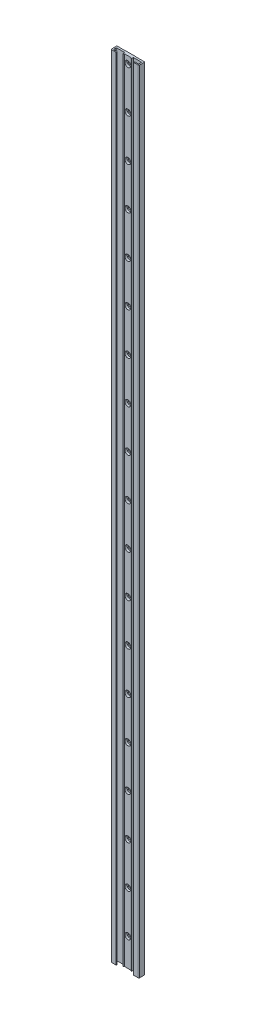
SolidWorks part; units mm, degrees
ref_plane "Front Plane" through (0, 0, 0) normal (0, 0, 1) x (1, 0, 0)
ref_plane "Top Plane" through (0, 0, 0) normal (0, 1, 0) x (1, 0, 0)
ref_plane "Right Plane" through (0, 0, 0) normal (1, 0, 0) x (0, 0, -1)
ref_plane "Plane4" through (0, 0, 8.7) normal (0, 0, 1) x (1, 0, 0)
sketch "Sketch1" plane through (0, 0, 8.7) normal (0, 0, 1) x (1, 0, 0)
  line L0 (-20, 0) -> (20, 0)
  line L1 (20, 0) -> (20, 1130.3)
  line L2 (20, 1130.3) -> (-20, 1130.3)
  line L3 (-20, 1130.3) -> (-20, 0)
  dimension "D1" = 1130.3
extrude "Boss-Extrude1" add sketch "Sketch1" against normal blind 8.7
sketch "Sketch2" plane through (0, 0, 0) normal (0, -1, 0) x (1, 0, 0)
  line L0 (12.5, 8.7) -> (-12.5, 8.7)
  line L1 (-12.5, 8.7) -> (-12.5, 7.2)
  line L2 (-12.5, 7.2) -> (-18, 7.2)
  line L3 (-18, 7.2) -> (-18, 2.8)
  line L4 (-18, 2.8) -> (-6.3, 2.8)
  line L5 (-6.3, 2.8) -> (-6.3, 5.5)
  line L6 (-6.3, 5.5) -> (-4.75, 5.5)
  line L7 (-4.75, 5.5) -> (-4.75, 4.5)
  line L8 (-4.75, 4.5) -> (4.75, 4.5)
  line L9 (4.75, 4.5) -> (4.75, 5.5)
  line L10 (4.75, 5.5) -> (6.3, 5.5)
  line L11 (6.3, 5.5) -> (6.3, 2.8)
  line L12 (6.3, 2.8) -> (18, 2.8)
  line L13 (18, 2.8) -> (18, 7.2)
  line L14 (18, 7.2) -> (12.5, 7.2)
  line L15 (12.5, 7.2) -> (12.5, 8.7)
extrude "Cut-Extrude1" cut sketch "Sketch2" against normal through all
sketch "Sketch3" plane through (0, 0, 0) normal (0, -1, 0) x (1, 0, 0)
  line L0 (8, 0.2) -> (8, 0)
  line L1 (8, 0) -> (20, 0)
  line L2 (20, 0) -> (20, 0.2)
  line L3 (20, 0.2) -> (8, 0.2)
extrude "Cut-Extrude2" cut sketch "Sketch3" against normal through all
sketch "Sketch4" plane through (0, 0, 0) normal (0, -1, 0) x (1, 0, 0)
  line L0 (-8, 0) -> (-8, 0.2)
  line L1 (-8, 0.2) -> (-20, 0.2)
  line L2 (-20, 0.2) -> (-20, 0)
  line L3 (-20, 0) -> (-8, 0)
extrude "Cut-Extrude3" cut sketch "Sketch4" against normal through all
draft "Draft1" type of draft neutral plane draft angle 45 faces to draft 2 face at (4.75, 565.15, 5) face at (-4.75, 565.15, 5) neutral plane through (-4.75, 1130.3, 4.5) neutral plane normal (0, 0, 1) parameters "D1"=45
hole_wizard "CBORE for M4 Hex Head Machine Screw1" positions "Sketch6" profile "Sketch5" counterbore size "M4" standard "ANSI Metric"
sketch "Sketch6" plane through (0, 0, 4.5) normal (0, 0, 1) x (1, 0, 0)
  point P0 (0, 160)
  point P1 (0, 100)
  point P2 (0, 40)
  point P12 (0, 220)
  point P13 (0, 280)
  point P14 (0, 340)
  point P15 (0, 400)
  point P16 (0, 460)
  point P17 (0, 520)
  point P18 (0, 580)
  point P19 (0, 640)
  point P20 (0, 700)
  point P21 (0, 760)
  point P22 (0, 820)
  point P23 (0, 880)
  point P24 (0, 940)
  point P25 (0, 1000)
  point P26 (0, 1060)
  point P27 (0, 1120)
  point P28 (0, 1180)
  dimension "D1" = 18
sketch "Sketch5" plane through (0, 160, 4.5) normal (1, 0, 0) x (0, -1, 0)
  line L0 (0, 0) -> (0, 4.5)
  line L1 (0, 4.5) -> (2.25, 4.5)
  line L3 (2.25, 4.5) -> (2.25, 3.1)
  line L4 (2.25, 3.1) -> (4.25, 3.1)
  line L5 (4.25, 3.1) -> (4.25, 0)
  line L7 (4.25, 0) -> (0, 0)
  line L11 (0, -6.35) -> (0, 107.95) construction
  dimension "Thru Hole Dia." = 4.5
  dimension "Thru Hole Depth" = 4.5
  dimension "C'Bore Dia." = 8.5
  dimension "C'Bore Depth" = 3.1
fillet "Fillet1" radius 0.5 6 edges at (-18, 565.15, 7.2) (-18, 565.15, 2.8) (-20, 565.15, 0.2) (18, 565.15, 7.2) (20, 565.15, 0.2) (18, 565.15, 2.8)
fillet "Fillet2" radius 1 2 edges at (20, 565.15, 8.7) (-20, 565.15, 8.7)
ref_plane "Mid_Plane" through (0, 0, 0) normal (1, 0, 0) x (0, 0, -1)
